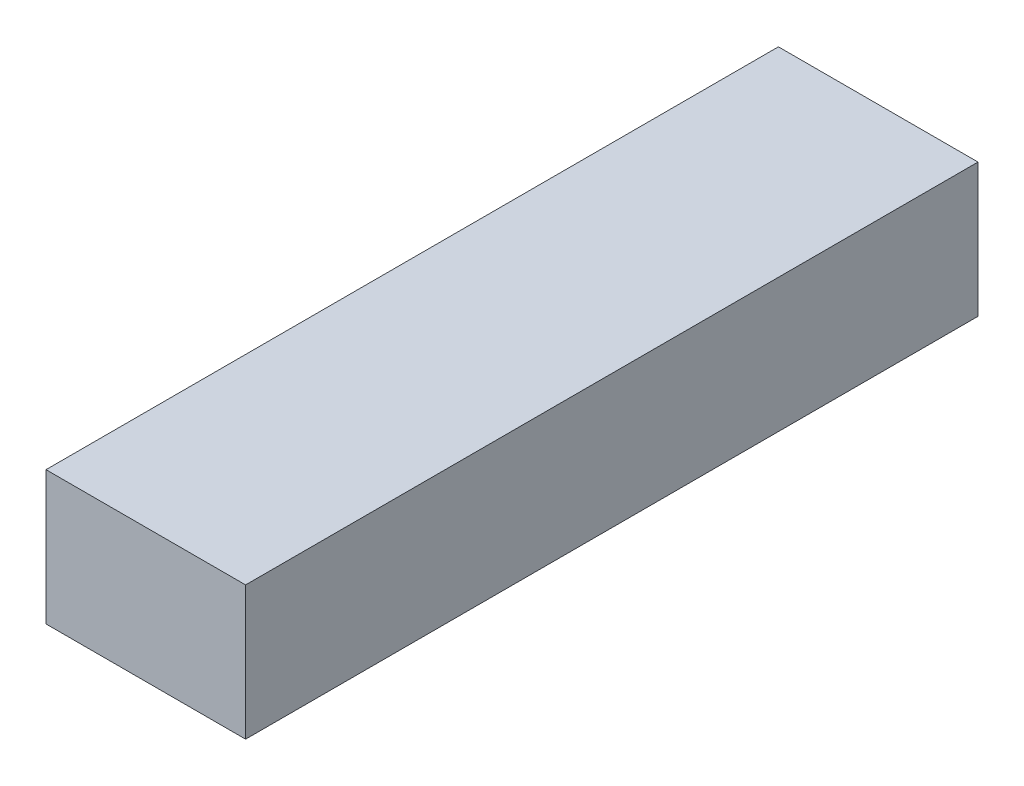
SolidWorks part; units mm, degrees
ref_plane "Alzado" through (0, 0, 0) normal (0, 0, 1) x (1, 0, 0)
ref_plane "Planta" through (0, 0, 0) normal (0, 1, 0) x (1, 0, 0)
ref_plane "Vista lateral" through (0, 0, 0) normal (1, 0, 0) x (0, 0, -1)
sketch "Croquis1" plane through (0, 0, 0) normal (0, 1, 0) x (1, 0, 0)
  line L1 (-14.986, -54.991) -> (14.986, -54.991)
  line L2 (-14.986, -54.991) -> (-14.986, 54.991)
  line L3 (-14.986, 54.991) -> (14.986, 54.991)
  line L4 (14.986, -54.991) -> (14.986, 54.991)
  line L5 (-14.986, -54.991) -> (14.986, 54.991) construction
  line L6 (-14.986, 54.991) -> (14.986, -54.991) construction
  point P0 (0, 0)
  dimension "D1" = 109.982
  dimension "D2" = 29.972
extrude "Saliente-Extruir1" add sketch "Croquis1" along normal blind 20.066
